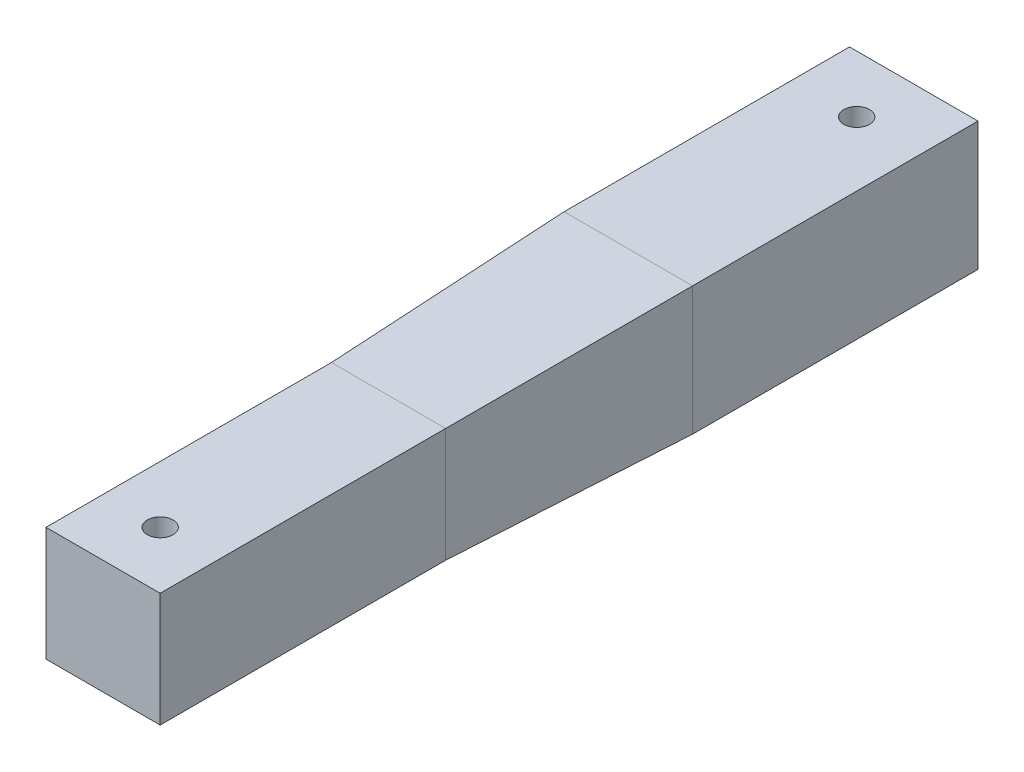
SolidWorks part; units mm, degrees
ref_plane "Plan de face" through (0, 0, 0) normal (0, 0, 1) x (1, 0, 0)
ref_plane "Plan de dessus" through (0, 0, 0) normal (0, 1, 0) x (1, 0, 0)
ref_plane "Plan de droite" through (0, 0, 0) normal (1, 0, 0) x (0, 0, -1)
sketch "Esquisse1" plane through (0, 0, 0) normal (0, 0, 1) x (1, 0, 0)
  line L1 (-42.865, 18) -> (-22.865, 18)
  line L2 (-42.865, 18) -> (-42.865, -2)
  line L3 (-42.865, -2) -> (-22.865, -2)
  line L4 (-22.865, 18) -> (-22.865, -2)
  dimension "D1" = 20
  dimension "D2" = 20
extrude "Boss.-Extru.1" add sketch "Esquisse1" along normal blind 50
ref_plane "Plan1" through (0, 0, -92) normal (0, 0, -1) x (-1, 0, 0)
sketch "Esquisse2" plane through (0, 0, -92) normal (0, 0, -1) x (-1, 0, 0)
  line L0 (42.865, 18) -> (22.865, -2) construction
  line L1 (44.115, 19.25) -> (21.615, 19.25)
  line L2 (44.115, 19.25) -> (44.115, -3.25)
  line L3 (44.115, -3.25) -> (21.615, -3.25)
  line L4 (21.615, 19.25) -> (21.615, -3.25)
  line L5 (42.865, -2) -> (22.865, 18) construction
  line L6 (44.115, 19.25) -> (21.615, -3.25) construction
  line L7 (44.115, -3.25) -> (21.615, 19.25) construction
  point P12 (32.865, 8)
  point P13 (32.865, 8)
  dimension "D1" = 22.5
  dimension "D2" = 22.5
extrude "Boss.-Extru.2" add sketch "Esquisse2" against normal blind 50 separate body
sketch "Esquisse4" plane through (0, 0, 0) normal (0, 0, -1) x (-1, 0, 0)
  line L1 (42.865, 18) -> (22.865, 18)
  line L2 (42.865, 18) -> (42.865, -2)
  line L3 (42.865, -2) -> (22.865, -2)
  line L4 (22.865, 18) -> (22.865, -2)
sketch "Esquisse5" plane through (0, 0, -42) normal (0, 0, 1) x (1, 0, 0)
  line L1 (-44.115, 19.25) -> (-21.615, 19.25)
  line L2 (-44.115, 19.25) -> (-44.115, -3.25)
  line L3 (-44.115, -3.25) -> (-21.615, -3.25)
  line L4 (-21.615, 19.25) -> (-21.615, -3.25)
loft "Lissage1" add profiles "Esquisse5", "Esquisse4"
sketch "Esquisse6" plane through (0, 19.25, 0) normal (0, 1, 0) x (1, 0, 0)
  line L0 (-44.115, 92) -> (-21.615, 92) construction
  line L1 (-21.615, 42) -> (-21.615, 92) construction
  circle A0 centre (-32.865, 82) radius 2.25
  dimension "D3" = 4.5
  dimension "D1" = 10
  dimension "D2" = 11.25
extrude "Enlèv. mat.-Extru.1" cut sketch "Esquisse6" against normal up to next
sketch "Esquisse7" plane through (0, -2, 0) normal (0, -1, 0) x (1, 0, 0)
  line L0 (-42.865, 50) -> (-22.865, 50) construction
  line L1 (-42.865, 50) -> (-42.865, 0) construction
  circle A0 centre (-32.865, 40) radius 2.25
  dimension "D3" = 4.5
  dimension "D1" = 10
  dimension "D2" = 10
extrude "Enlèv. mat.-Extru.2" cut sketch "Esquisse7" against normal up to next
